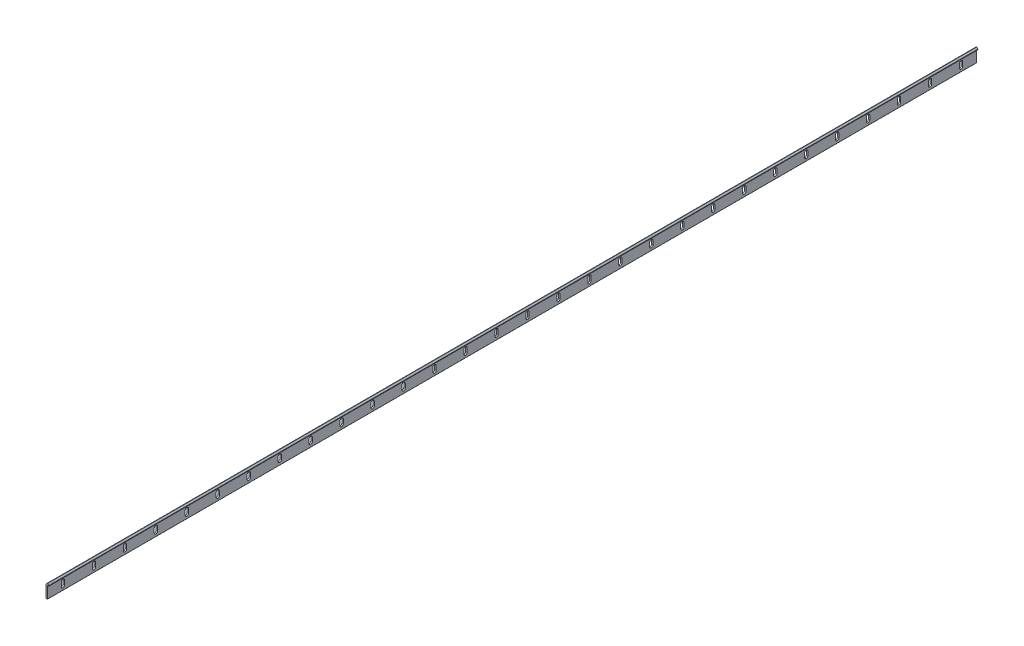
SolidWorks part; units mm, degrees
material "6061-T6 (SS)"
ref_plane "Front Plane" through (0, 0, 0) normal (0, 0, 1) x (1, 0, 0)
ref_plane "Top Plane" through (0, 0, 0) normal (0, 1, 0) x (1, 0, 0)
ref_plane "Right Plane" through (0, 0, 0) normal (1, 0, 0) x (0, 0, -1)
sketch "Sketch1" plane through (0, 0, 0) normal (0, 0, 1) x (1, 0, 0)
  line L0 (0, 20.3302) -> (2.0196, 22.3498)
  line L1 (0, 0) -> (2.375, 0)
  line L2 (0, 20.3302) -> (0, 0)
  line L4 (2.375, 0) -> (2.375, 19.5291)
  line L5 (2.375, 19.5291) -> (4.75, 19.5291)
  line L7 (2.7304, 22.3498) -> (4.75, 20.3302)
  line L8 (4.75, 19.5291) -> (4.75, 20.3302)
  arc A0 (2.7304, 22.3498) -> (2.0196, 22.3498) centre (2.375, 21.9944) ccw
  point P9 (2.375, 22.7052)
  dimension "D5" = 0.5026
  dimension "D6" = 22.497
  dimension "D1" = 2.375
  dimension "D2" = 19.5291
  dimension "D3" = 2.375
  dimension "D4" = 2.9679
extrude "Boss-Extrude1" add sketch "Sketch1" along normal blind 1500
fillet "Fillet1" radius 0.5033 1 edges at (0, 20.3302, 750)
fillet "Fillet2" radius 0.504 1 edges at (4.75, 20.3302, 750)
fillet "Fillet3" radius 0.3016 1 edges at (4.75, 19.5291, 750)
fillet "Fillet4" radius 0.3016 2 edges at (0, 0, 750) (2.375, 0, 750)
sketch "Sketch2" plane through (0, 0, 0) normal (-1, 0, 0) x (0, 0, 1)
  line L0 (25, 13.1043) -> (25, 6.4043) construction
  line L1 (27.65, 13.1043) -> (27.65, 6.4043)
  line L2 (22.35, 13.1043) -> (22.35, 6.4043)
  line L3 (1500, 0) -> (0, 0) construction
  line L4 (0, 20.1217) -> (0, 0.3016) construction
  arc A0 (27.65, 13.1043) -> (22.35, 13.1043) centre (25, 13.1043) ccw
  arc A1 (22.35, 6.4043) -> (27.65, 6.4043) centre (25, 6.4043) ccw
  point P2 (25, 9.7543)
  dimension "D3" = 9.7543
  dimension "D1" = 5.3
  dimension "D2" = 6.7
  dimension "D4" = 25
extrude "Cut-Extrude1" cut sketch "Sketch2" against normal up to next (2.375 mm away)
pattern_linear "LPattern1" count 30 spacing 50 along (0, 0, 1) of "Cut-Extrude1"
equation "\"D3@Sketch1\"=\"D1@Sketch1\""
